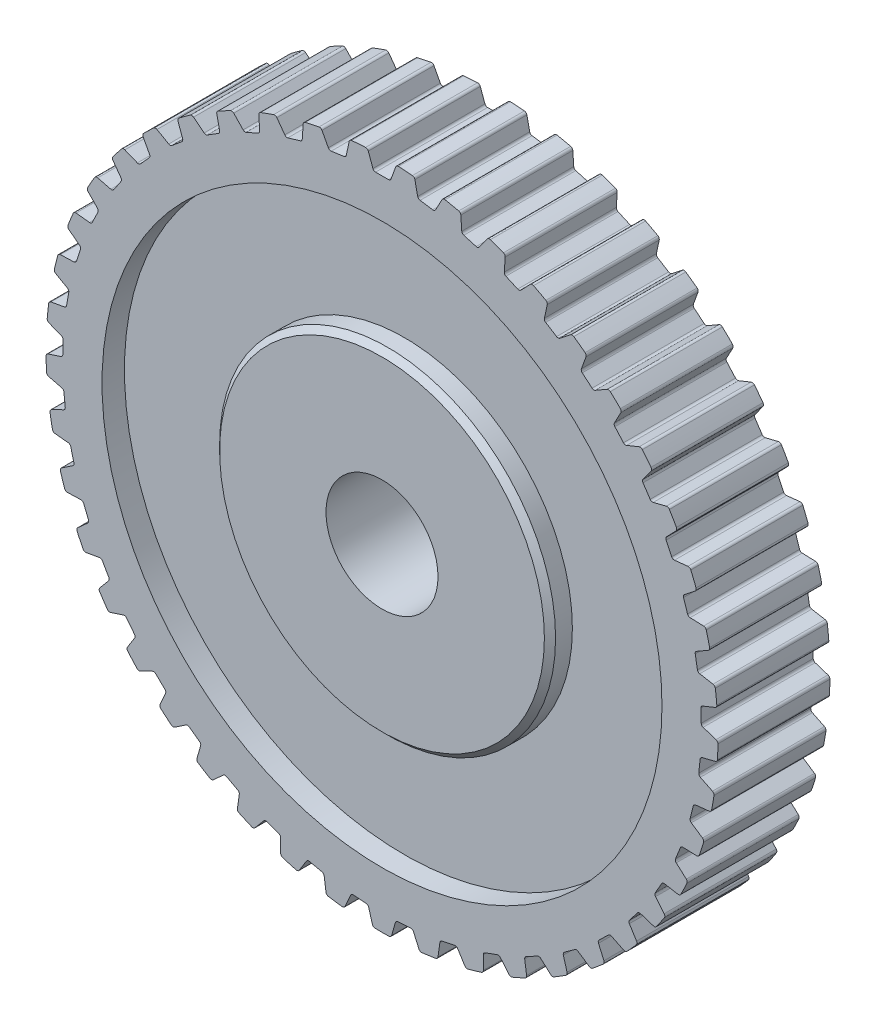
SolidWorks part; units mm, degrees
ref_plane "Front Plane" through (0, 0, 0) normal (0, 0, 1) x (1, 0, 0)
ref_plane "Top Plane" through (0, 0, 0) normal (0, 1, 0) x (1, 0, 0)
ref_plane "Right Plane" through (0, 0, 0) normal (1, 0, 0) x (0, 0, -1)
sketch "Sketch2" plane through (0, 0, 0) normal (0, 0, 1) x (1, 0, 0)
  line L0 (0, 0) -> (0, 8.282) construction
  line L3 (2, 4.5826) -> (2, 7)
  line L4 (2, 7) -> (-2, 7)
  line L5 (-2, 4.5826) -> (-2, 7)
  line L6 (0, 5) -> (-2, 7) construction
  line L7 (2, 7) -> (0, 5) construction
  circle A0 centre (0, 0) radius 30
  arc A1 (-2, 4.5826) -> (2, 4.5826) centre (0, 0) ccw
  point P4 (0, 5)
  dimension "D1" = 60
  dimension "D2" = 10
  dimension "D3" = 4
  dimension "D4" = 7
extrude "Boss-Extrude1" add sketch "Sketch2" along normal blind 10
sketch "Sketch3" plane through (0, 0, 10) normal (0, 0, 1) x (1, 0, 0)
  line L0 (0, 0) -> (0, 30) construction
  line L1 (-0.75, 28.5) -> (0.75, 28.5)
  line L2 (0.75, 28.5) -> (1.2859, 29.9724)
  line L3 (-0.75, 28.5) -> (-1.2859, 29.9724)
  circle A0 centre (0, 0) radius 30 construction
  circle M5 centre (0, 0) radius 30
  dimension "D1" = 1.5
  dimension "D2" = 0.75
  dimension "D3" = 110
  dimension "D4" = 110
  dimension "D5" = 28.5
extrude "Cut-Extrude1" cut sketch "Sketch3" against normal through all and the other way through all contours L1 L0 L3 M5 | L0 L1 L2 M5
pattern_circular "CirPattern1" count 45 over 360 about axis through (0, 0, 0) along (0, 0, 1) of "Cut-Extrude1"
sketch "Sketch4" plane through (0, 0, 10) normal (0, 0, 1) x (1, 0, 0)
  circle A0 centre (0, 0) radius 25
  dimension "D1" = 50
extrude "Cut-Extrude-Thin1" cut sketch "Sketch4" against normal blind 2 thin thin type one direction reverse wall 10
chamfer "Chamfer1" distance 0.5 angle 45 1 edges at (15, 0, 10)
ref_plane "Plane1" through (0, 0, 5) normal (0, 0, 1) x (1, 0, 0)
mirror "Mirror1" about plane through (0, 0, 5) normal (0, 0, 1) of "Cut-Extrude-Thin1"
chamfer "Chamfer2" distance 0.5 angle 45 1 edges at (15, 0, 0)
fillet "Fillet1" radius 0.25 110 edges at (-24.3067, -14.8995, 5) (-21.9966, -18.1374, 5) (-14.0422, -24.8119, 5) (-12.7177, -25.5161, 5) (-10.4523, -26.5247, 5) (-6.6591, -27.7213, 5) (-2.7362, -28.3783, 5) (-1.2399, -28.4829, 5) (2.7362, -28.3783, 5) (5.1919, -28.0331, 5) (14.0422, -24.8119, 5) (19.2583, -21.0222, 5) (22.9201, -16.9553, 5) (24.3067, -14.8995, 5) (25.0567, -13.6005, 5) (26.7057, -9.9809, 5) (27.472, -7.6225, 5) (27.8349, -6.1671, 5) (28.2655, -3.725, 5) (28.4223, -2.2332, 5) (28.4565, 1.7442, 5) (28.1973, 4.2104, 5) (26.8733, 9.5203, 5) (25.9444, 11.8195, 5) (25.2869, 13.1677, 5) (24.047, 15.3152, 5) (20.6778, 19.6276, 5) (18.894, 21.3502, 5) (17.7449, 22.3144, 5) (15.7387, 23.7719, 5) (12.2772, 25.731, 5) (10.9068, 26.3411, 5) (4.7091, 28.1183, 5) (-0.75, 28.5, 5) (-8.5766, 27.1892, 5) (-10.9068, 26.3411, 5) (-12.2772, 25.731, 5) (-14.4667, 24.5668, 5) (-15.7387, 23.7719, 5) (-17.7449, 22.3144, 5) (-18.894, 21.3502, 5) (-20.6778, 19.6276, 5) (-21.6815, 18.5129, 5) (-23.2082, 16.5588, 5) (-24.047, 15.3152, 5) (-25.9444, 11.8195, 5) (-26.8733, 9.5203, 5) (-27.9368, 5.6876, 5) (-28.4565, 1.7442, 5) (-28.5088, 0.2451, 5) (-28.2655, -3.725, 5)
sketch "Sketch5" plane through (0, 0, 10) normal (0, 0, 1) x (1, 0, 0)
  line L0 (-2, 7) -> (2, 7)
  line L1 (2, 7) -> (2, 4.5826)
  line L2 (-2, 7) -> (-2, 4.5826)
  arc A0 (2, 4.5826) -> (-2, 4.5826) centre (0, 0) ccw
extrude "Boss-Extrude2" add sketch "Sketch5" against normal blind 10 contours A0 L2 L0 L1
